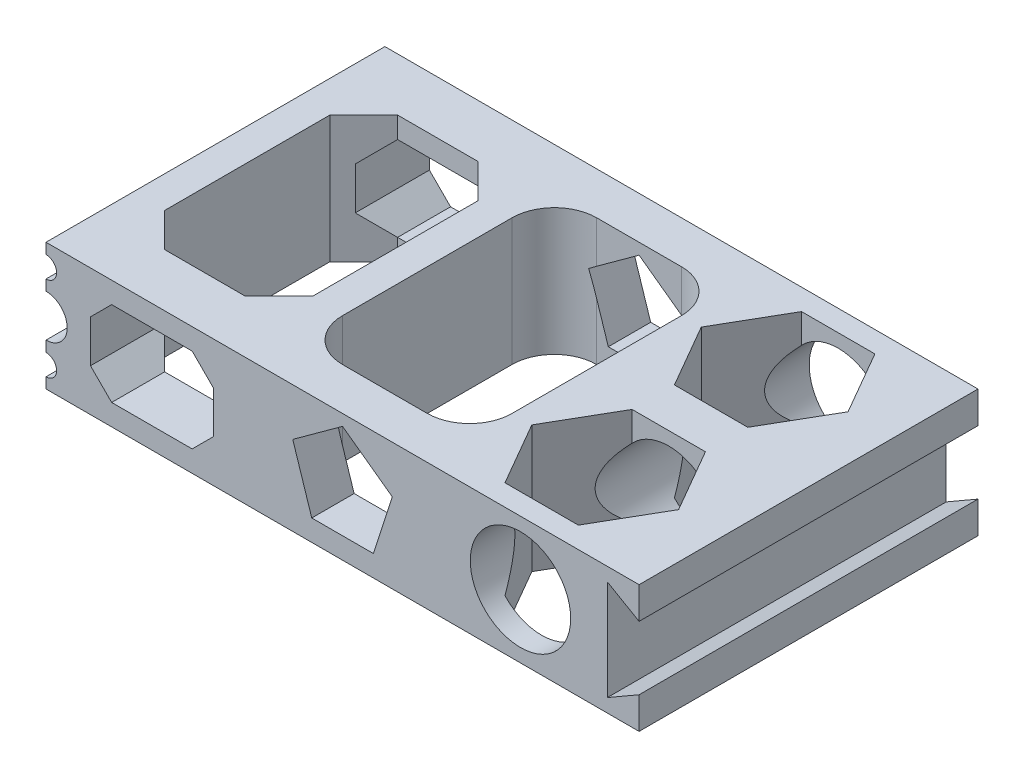
SolidWorks part; units mm, degrees
material "AISI 1020"
ref_plane "Front Plane" through (0, 0, 0) normal (0, 0, 1) x (1, 0, 0)
ref_plane "Top Plane" through (0, 0, 0) normal (0, 1, 0) x (1, 0, 0)
ref_plane "Right Plane" through (0, 0, 0) normal (1, 0, 0) x (0, 0, -1)
sketch "Sketch1" plane through (0, 0, 0) normal (0, 1, 0) x (1, 0, 0)
  line L1 (-88.9, 50.8) -> (88.9, 50.8)
  line L2 (-88.9, 50.8) -> (-88.9, -50.8)
  line L3 (-88.9, -50.8) -> (88.9, -50.8)
  line L4 (88.9, 50.8) -> (88.9, -50.8)
  line L5 (-88.9, 50.8) -> (88.9, -50.8) construction
  line L6 (-88.9, -50.8) -> (88.9, 50.8) construction
  point P0 (0, 0)
  dimension "D1" = 101.6
  dimension "D2" = 177.8
extrude "Boss-Extrude1" add sketch "Sketch1" along normal mid plane 38.1
sketch "Sketch2" plane through (0, 19.05, 0) normal (0, 1, 0) x (1, 0, 0)
  line L0 (-79.375, 24.765) -> (-69.215, 34.925)
  line L1 (-69.215, 34.925) -> (-45.085, 34.925)
  line L2 (-45.085, 34.925) -> (-34.925, 24.765)
  line L3 (-34.925, 24.765) -> (-34.925, -24.765)
  line L4 (-34.925, -24.765) -> (-45.085, -34.925)
  line L5 (-45.085, -34.925) -> (-69.215, -34.925)
  line L6 (-69.215, -34.925) -> (-79.375, -24.765)
  line L7 (-79.375, -24.765) -> (-79.375, 24.765)
  line L8 (-88.9, -50.8) -> (88.9, -50.8) construction
  line L9 (-88.9, 50.8) -> (-88.9, -50.8) construction
  line L10 (88.9, 50.8) -> (-88.9, 50.8) construction
  line L11 (-12.7, 38.1) -> (12.7, 38.1)
  line L12 (-25.4, 25.4) -> (-25.4, -25.4)
  line L13 (-12.7, -38.1) -> (12.7, -38.1)
  line L14 (25.4, 25.4) -> (25.4, -25.4)
  line L15 (-25.4, 38.1) -> (25.4, -38.1) construction
  line L16 (-25.4, -38.1) -> (25.4, 38.1) construction
  line L17 (64.3385, 6.35) -> (75.337, 25.4)
  line L18 (75.337, 25.4) -> (64.3385, 44.45)
  line L19 (64.3385, 44.45) -> (42.3415, 44.45)
  line L20 (42.3415, 44.45) -> (31.343, 25.4)
  line L21 (31.343, 25.4) -> (42.3415, 6.35)
  line L22 (42.3415, 6.35) -> (64.3385, 6.35)
  line L24 (88.9, -50.8) -> (88.9, 50.8) construction
  line L25 (-20.955, 0) -> (20.955, 0) construction
  line L26 (42.3415, -6.35) -> (64.3385, -6.35)
  line L27 (31.343, -25.4) -> (42.3415, -6.35)
  line L28 (42.3415, -44.45) -> (31.343, -25.4)
  line L29 (64.3385, -44.45) -> (42.3415, -44.45)
  line L30 (75.337, -25.4) -> (64.3385, -44.45)
  line L31 (64.3385, -6.35) -> (75.337, -25.4)
  arc A0 (12.7, -38.1) -> (25.4, -25.4) centre (12.7, -25.4) ccw
  arc A1 (-25.4, -25.4) -> (-12.7, -38.1) centre (-12.7, -25.4) ccw
  arc A2 (12.7, 38.1) -> (25.4, 25.4) centre (12.7, 25.4) cw
  arc A3 (-12.7, 38.1) -> (-25.4, 25.4) centre (-12.7, 25.4) ccw
  circle A4 centre (53.34, 25.4) radius 19.05 construction
  circle A5 centre (53.34, -25.4) radius 19.05 construction
  point P12 (0, 0)
  dimension "D6" = 12.7
  dimension "D1" = 10.16
  dimension "D2" = 15.875
  dimension "D3" = 85.725
  dimension "D4" = 44.45
  dimension "D5" = 9.525
  dimension "D7" = 76.2
  dimension "D8" = 12.7
  dimension "D9" = 50.8
  dimension "D10" = 63.5
  dimension "D11" = 38.1
  dimension "D12" = 35.56
  dimension "D13" = 76.2
extrude "Cut-Extrude1" cut sketch "Sketch2" against normal through all
sketch "Sketch3" plane through (0, 0, 50.8) normal (0, 0, 1) x (1, 0, 0)
  line L0 (-88.9, 19.05) -> (-88.9, -19.05) construction
  line L1 (-88.9, 19.05) -> (88.9, 19.05) construction
  line L2 (-75.565, 6.35) -> (-69.215, 12.7)
  line L3 (-88.9, -19.05) -> (88.9, -19.05) construction
  line L12 (-69.215, 12.7) -> (-45.085, 12.7)
  line L13 (-75.565, 6.35) -> (-75.565, -6.35)
  line L14 (-69.215, -12.7) -> (-45.085, -12.7)
  line L15 (-38.735, 6.35) -> (-38.735, -6.35)
  line L16 (-75.565, 12.7) -> (-38.735, -12.7) construction
  line L17 (-75.565, -12.7) -> (-38.735, 12.7) construction
  line L18 (-45.085, 12.7) -> (-38.735, 6.35)
  line L19 (-75.565, -6.35) -> (-69.215, -12.7)
  line L20 (-45.085, -12.7) -> (-38.735, -6.35)
  line L22 (9.2271, -12.7) -> (14.9297, 4.851)
  line L23 (14.9297, 4.851) -> (0, 15.6981)
  line L24 (0, 15.6981) -> (-14.9297, 4.851)
  line L25 (-14.9297, 4.851) -> (-9.2271, -12.7)
  line L26 (-9.2271, -12.7) -> (9.2271, -12.7)
  line L30 (88.9, 9.525) -> (79.375, 15.0243)
  line L31 (88.9, 19.05) -> (88.9, -19.05) construction
  line L32 (79.375, 15.0243) -> (79.375, -15.0243)
  line L33 (79.375, -15.0243) -> (88.9, -9.525)
  line L34 (88.9, 9.525) -> (88.9, -9.525)
  circle A0 centre (-88.9, 12.7) radius 3.175
  circle A1 centre (-88.9, 0) radius 6.35
  circle A2 centre (-88.9, -12.7) radius 3.175
  circle A3 centre (0, 0) radius 12.7 construction
  circle A4 centre (53.34, 0) radius 15.0495
  point P12 (-57.15, 0)
  dimension "D1" = 6.35
  dimension "D3" = 6.35
  dimension "D4" = 12.7
  dimension "D19" = 53.34
  dimension "D20" = 30.099
  dimension "D2" = 6.35
  dimension "D5" = 50.165
  dimension "D6" = 13.335
  dimension "D7" = 25.4
  dimension "D8" = 6.35
  dimension "D9" = 6.35
  dimension "D10" = 45
  dimension "D11" = 6.35
  dimension "D12" = 45
  dimension "D13" = 6.35
  dimension "D14" = 45
  dimension "D15" = 6.35
  dimension "D16" = 45
  dimension "D17" = 12.7
  dimension "D18" = 72
  dimension "D21" = 9.525
  dimension "D22" = 9.525
  dimension "D23" = 60
  dimension "D24" = 60
  dimension "D25" = 9.525
extrude "Cut-Extrude2" cut sketch "Sketch3" against normal through all
